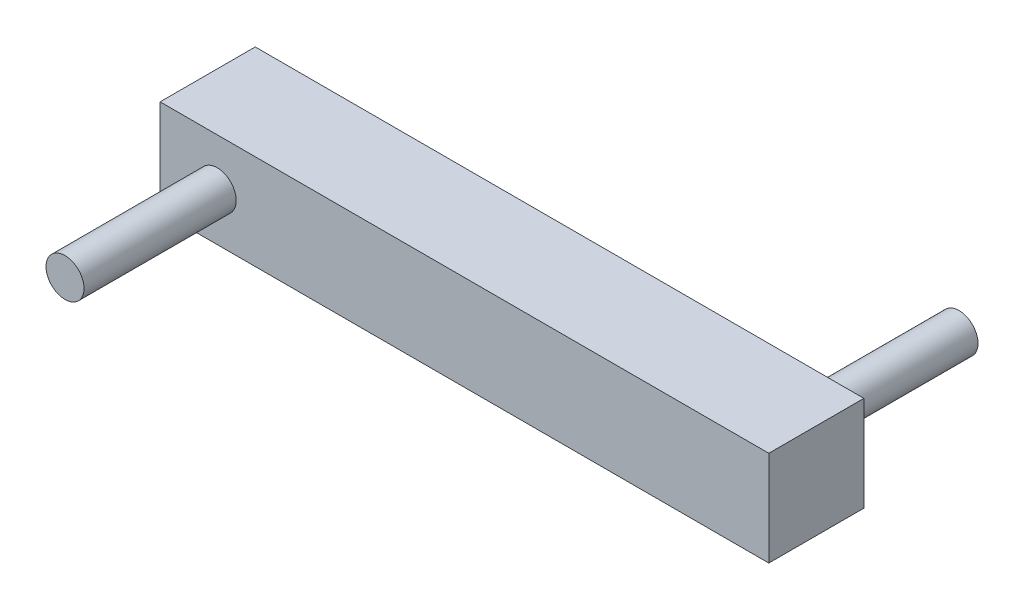
SolidWorks part; units mm, degrees
ref_plane "Front Plane" through (0, 0, 0) normal (0, 0, 1) x (1, 0, 0)
ref_plane "Top Plane" through (0, 0, 0) normal (0, 1, 0) x (1, 0, 0)
ref_plane "Right Plane" through (0, 0, 0) normal (1, 0, 0) x (0, 0, -1)
sketch "Sketch1" plane through (0, 0, 0) normal (0, 0, 1) x (1, 0, 0)
  line L1 (0, 0) -> (16, 0)
  line L2 (0, 0) -> (0, 2.5)
  line L3 (0, 2.5) -> (16, 2.5)
  line L4 (16, 0) -> (16, 2.5)
  point P9 (1.5, 1.25)
  point P10 (14.5, 1.25)
  point P11 (0, 0)
  dimension "D6" = 1.25
  dimension "D1" = 16
  dimension "D2" = 2.5
  dimension "D3" = 1.5
  dimension "D4" = 1.5
extrude "Boss-Extrude1" add sketch "Sketch1" along normal mid plane 2.5
sketch "Sketch2" plane through (0, 0, 1.25) normal (0, 0, 1) x (1, 0, 0)
  circle A0 centre (1.5, 1.25) radius 0.5
  dimension "D1" = 1
extrude "Boss-Extrude2" add sketch "Sketch2" along normal blind 4
sketch "Sketch3" plane through (0, 0, -1.25) normal (0, 0, -1) x (-1, 0, 0)
  circle A0 centre (-14.5, 1.25) radius 0.5
  dimension "D1" = 1
extrude "Boss-Extrude3" add sketch "Sketch3" along normal blind 4
